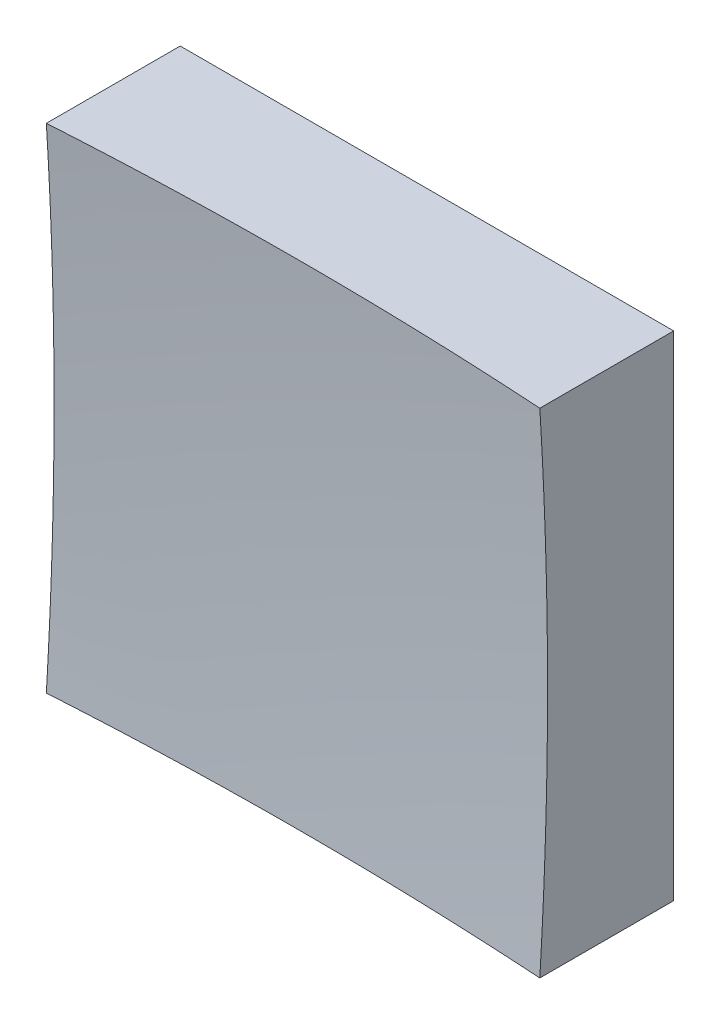
SolidWorks part; units mm, degrees
ref_plane "前视基准面" through (0, 0, 0) normal (0, 0, 1) x (1, 0, 0)
ref_plane "上视基准面" through (0, 0, 0) normal (0, 1, 0) x (1, 0, 0)
ref_plane "右视基准面" through (0, 0, 0) normal (1, 0, 0) x (0, 0, -1)
sketch "草图1" plane through (0, 0, 0) normal (0, 0, 1) x (1, 0, 0)
  line L1 (-6.25, 6.25) -> (6.25, 6.25)
  line L2 (-6.25, 6.25) -> (-6.25, -6.25)
  line L3 (-6.25, -6.25) -> (6.25, -6.25)
  line L4 (6.25, 6.25) -> (6.25, -6.25)
  line L5 (-6.25, 6.25) -> (6.25, -6.25) construction
  line L6 (-6.25, -6.25) -> (6.25, 6.25) construction
  point P0 (0, 0)
  dimension "D1" = 12.5
  dimension "D2" = 12.5
extrude "凸台-拉伸1" add sketch "草图1" along normal blind 10 contours L2 L3 L4 L1
sketch "草图2" plane through (0, 0, 0) normal (0, 1, 0) x (1, 0, 0)
  line L0 (-7.4603, -3) -> (7.3192, -3) construction
  line L1 (0, 0) -> (0, -12.1749) construction
  line L2 (97.4845, -80.7118) -> (0, -80.7118)
  line L3 (0, -80.7118) -> (0, -3)
  arc A1 (97.4845, -80.7118) -> (0, -3) centre (0, -103) ccw
  dimension "D2" = 200
  dimension "D1" = 3
revolve "切除-旋转2" cut sketch "草图2" angle 360 about L3
